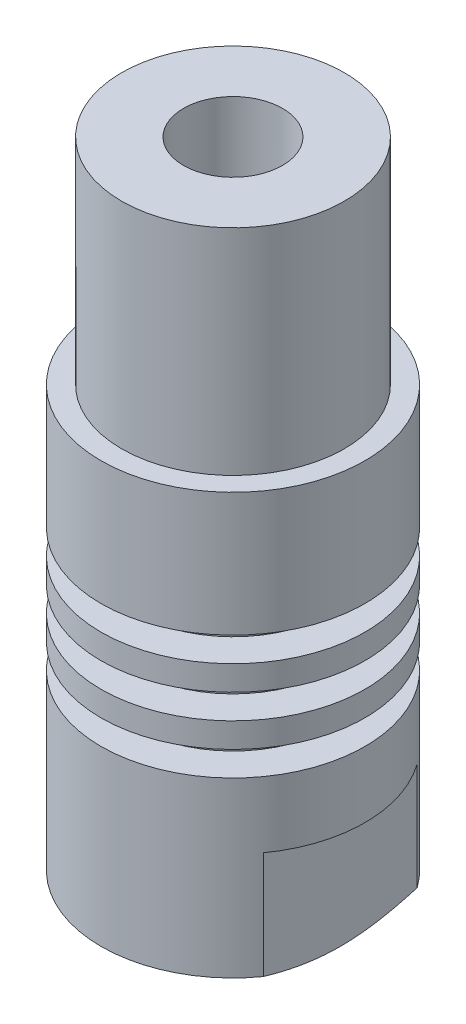
SolidWorks part; units mm, degrees
material "Gomma"
ref_plane "Piano frontale" through (0, 0, 0) normal (0, 0, 1) x (1, 0, 0)
ref_plane "Piano superiore" through (0, 0, 0) normal (0, 1, 0) x (1, 0, 0)
ref_plane "Piano destro" through (0, 0, 0) normal (1, 0, 0) x (0, 0, -1)
sketch "Schizzo1" plane through (0, 0, 0) normal (0, 0, 1) x (1, 0, 0)
  line L0 (0, 0) -> (-5, 0)
  line L1 (-5, 0) -> (-8, 1.5)
  line L2 (-8, 1.5) -> (-8, 12)
  line L3 (-8, 12) -> (-6, 12)
  line L4 (-6, 12) -> (-6, 13.5)
  line L5 (-6, 13.5) -> (-8, 13.5)
  line L6 (-8, 13.5) -> (-8, 15)
  line L7 (-8, 15) -> (-6, 15)
  line L8 (-6, 15) -> (-6, 16.5)
  line L9 (-6, 16.5) -> (-8, 16.5)
  line L10 (-8, 16.5) -> (-8, 18)
  line L11 (-8, 18) -> (-6, 18)
  line L12 (-6, 18) -> (-6, 19.5)
  line L13 (-6, 19.5) -> (-8, 19.5)
  line L14 (-8, 19.5) -> (-8, 27)
  line L15 (-8, 40) -> (0, 40)
  line L18 (-8, 27) -> (-8, 40)
  line L20 (0, 40) -> (0, 0)
  line L21 (0, 129.4074) -> (0, -17.2322) construction
  dimension "D1" = 1.5
  dimension "D2" = 16
  dimension "D3" = 2
  dimension "D4" = 40
  dimension "D5" = 12
  dimension "D8" = 1.5
  dimension "D10" = 10
  dimension "D11" = 12
  dimension "D12" = 1.5
  dimension "D13" = 1.5
revolve "Rivoluzione1" add sketch "Schizzo1" angle 360 about L21
sketch "Schizzo2" plane through (0, 0, 0) normal (0, 0, 1) x (1, 0, 0)
  line L0 (-8, 8) -> (-6.5, 8)
  line L1 (-6.5, 8) -> (-6.5, 0)
  line L2 (-6.5, 0) -> (-8, 0)
  line L3 (-8, 0) -> (-8, 8)
  line L4 (6.5, 8) -> (6.5, 0)
  line L5 (6.5, 0) -> (8, 0)
  line L6 (8, 0) -> (8, 8)
  line L7 (8, 8) -> (6.5, 8)
  line L8 (0, 0) -> (0, 9.0399) construction
  line L9 (-5, 0) -> (5, 0) construction
  line L11 (8, 1.5) -> (8, 12) construction
  line L12 (-8, 12) -> (-8, 1.5) construction
  point P20 (-45.2048, 18.2929)
  point P21 (-40.6745, 40.485)
  point P24 (-39.0987, 37.4647)
  dimension "D2" = 1.5
extrude "Taglio-Estrusione1" cut sketch "Schizzo2" against normal up to next and the other way up to next
sketch "Schizzo7" plane through (0, 40, 0) normal (0, 1, 0) x (1, 0, 0)
  circle A0 centre (0, 0) radius 3
extrude "Taglio-Estrusione2" cut sketch "Schizzo7" against normal through all
hole_wizard "Foro filettato M8-1" positions "Schizzo9" profile "Schizzo8" tap size "M8" standard "ISO"
sketch "Schizzo9" plane through (0, 0, 0) normal (0, -1, 0) x (-1, 0, 0)
  point P0 (0, 0)
sketch "Schizzo8" plane through (0, 0, 0) normal (1, 0, 0) x (0, 0, -1)
  line L0 (0, 0) -> (0, 14.0429)
  line L1 (0, 14.0429) -> (3.4, 12)
  line L2 (3.4, 12) -> (3.4, 0)
  line L5 (3.4, 0) -> (0, 0)
  line L10 (0, 14.0429) -> (-3.4, 12) construction
  line L11 (0, -6.35) -> (0, 107.95) construction
  dimension "Tap Drill Dia." = 6.8
  dimension "Tap Drill Depth" = 12
  dimension "Drill Angle" = 118
cosmetic thread "Filettatura del foro3" parameters "D1"=12, "D2"=8
sketch "Schizzo10" plane through (0, 40, 0) normal (0, 1, 0) x (1, 0, 0)
  circle A0 centre (0, 0) radius 6.75
  dimension "D1" = 13.5
extrude "Taglio-Estrusione3" cut sketch "Schizzo10" against normal blind 13 flip side to cut
